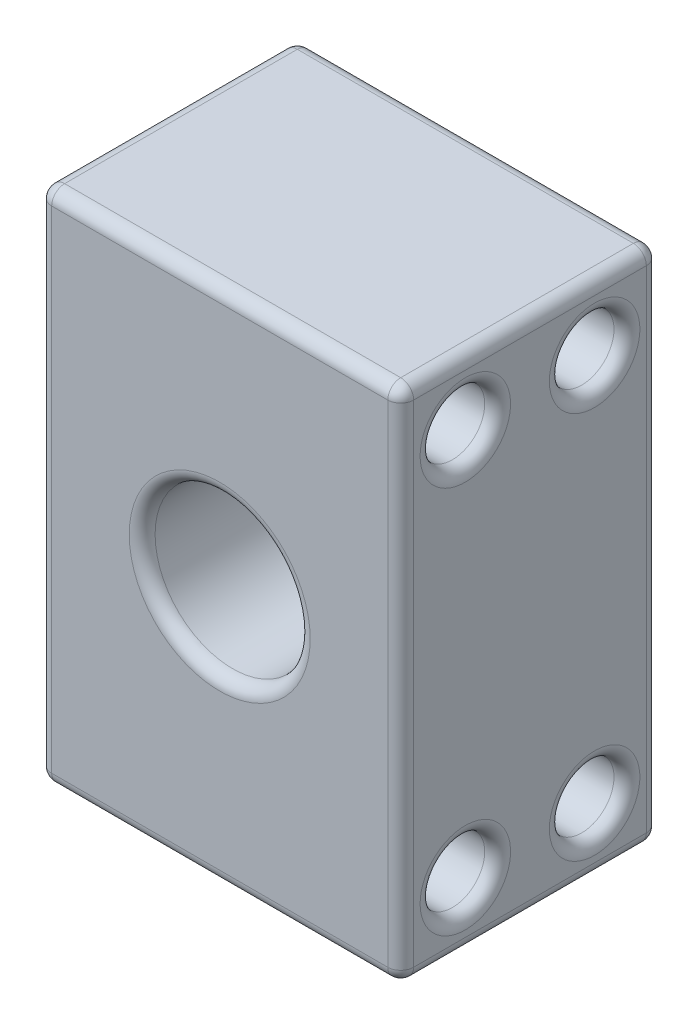
SolidWorks part; units mm, degrees
material "PET"
ref_plane "Front Plane" through (0, 0, 0) normal (0, 0, 1) x (1, 0, 0)
ref_plane "Top Plane" through (0, 0, 0) normal (0, 1, 0) x (1, 0, 0)
ref_plane "Right Plane" through (0, 0, 0) normal (1, 0, 0) x (0, 0, -1)
sketch "Sketch1" plane through (0, 0, 0) normal (0, 0, 1) x (1, 0, 0)
  line L1 (0, 0) -> (28, 0)
  line L2 (0, 0) -> (0, 40)
  line L3 (0, 40) -> (28, 40)
  line L4 (28, 0) -> (28, 40)
  dimension "D1" = 40
  dimension "D2" = 28
extrude "Boss-Extrude1" add sketch "Sketch1" along normal blind 20
sketch "Sketch2" plane through (0, 0, 20) normal (0, 0, 1) x (1, 0, 0)
  line L0 (0, 0) -> (28, 0) construction
  circle A0 centre (14, 20) radius 6
  point P4 (14, 0)
  dimension "D2" = 12
  dimension "D1" = 20
extrude "Cut-Extrude1" cut sketch "Sketch2" against normal blind 12
sketch "Sketch3" plane through (28, 0, 0) normal (1, 0, 0) x (0, 0, -1)
  line L0 (-22.2625, 20) -> (-6.5962, 20) construction
  line L1 (0, 0) -> (0, 40) construction
  line L2 (-20, 0) -> (-20, 40) construction
  circle A0 centre (-15, 35) radius 2.5
  circle A1 centre (-5, 35) radius 2.5
  circle A2 centre (-5, 5) radius 2.5
  circle A3 centre (-15, 5) radius 2.5
  point P15 (0, 20)
  dimension "D1" = 5
  dimension "D2" = 10
  dimension "D3" = 15
  dimension "D4" = 5
extrude "Cut-Extrude2" cut sketch "Sketch3" against normal through all
fillet "Fillet1" radius 1 22 edges at (20, 20, 8) (28, 20, 20) (0, 20, 20) (20, 20, 20) (28, 20, 0) (0, 20, 0) (0, 0, 10) (14, 0, 20) (28, 0, 10) (14, 0, 0) (28, 40, 10) (14, 40, 20) (0, 40, 10) (14, 40, 0) (0, 35, 12.5) (0, 35, 2.5) (0, 5, 7.5) (0, 5, 17.5) (28, 35, 12.5) (28, 35, 2.5) (28, 5, 7.5) (28, 5, 17.5)
